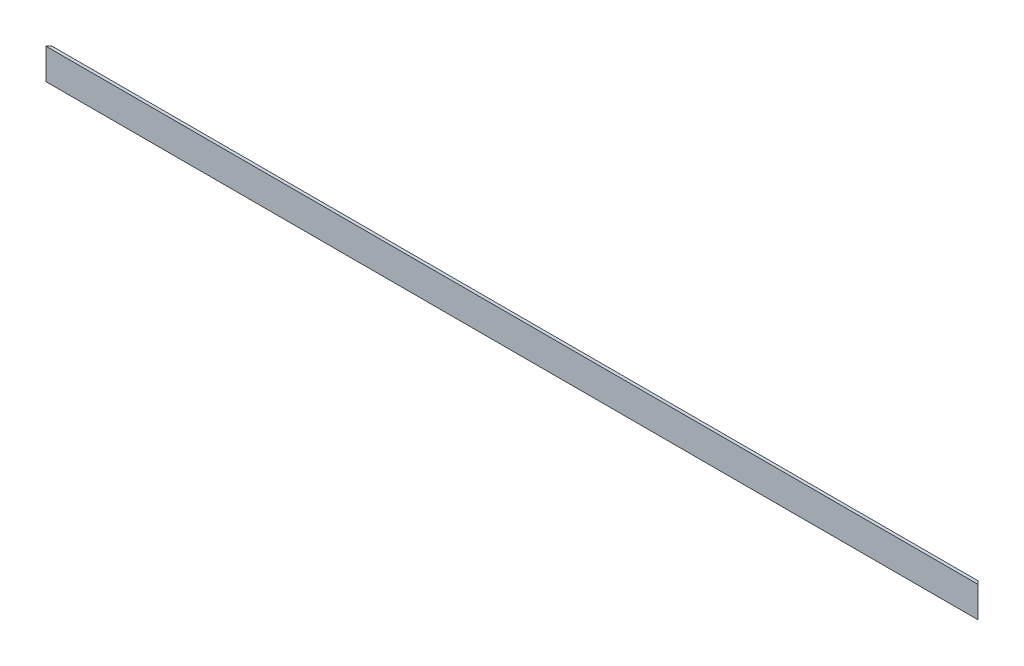
SolidWorks part; units mm, degrees
ref_plane "Спереди" through (0, 0, 0) normal (0, 0, 1) x (1, 0, 0)
ref_plane "Сверху" through (0, 0, 0) normal (0, 1, 0) x (1, 0, 0)
ref_plane "Справа" through (0, 0, 0) normal (1, 0, 0) x (0, 0, -1)
sketch "Эскиз1" plane through (0, 0, 0) normal (1, 0, 0) x (0, 0, -1)
  line L0 (0, 0) -> (0, 15)
  line L1 (0, 15) -> (1.5, 15)
  line L2 (1.5, 15) -> (1.5, 1.5)
  line L3 (1.5, 1.5) -> (15, 1.5)
  line L4 (15, 1.5) -> (15, 0)
  line L5 (15, 0) -> (0, 0)
  dimension "D1" = 15
  dimension "D2" = 15
  dimension "D3" = 1.5
  dimension "D4" = 1.5
extrude "Бобышка-Вытянуть1" add sketch "Эскиз1" along normal blind 455
sketch "Эскиз2" plane through (0, 0, 0) normal (0, -1, 0) x (1, 0, 0)
  line L0 (455, 0) -> (434.1738, -20.8262)
  line L1 (434.1738, -20.8262) -> (455, -20.8262)
  line L2 (455, -20.8262) -> (455, 0)
  dimension "D1" = 45
ref_plane "Плоскость1" through (227.5, 0, 0) normal (1, 0, 0) x (0, 0, -1)
extrude "Вырез-Вытянуть1" cut sketch "Эскиз2" against normal through all
mirror "Зеркальное отражение1" about plane through (227.5, 0, 0) normal (1, 0, 0) of "Вырез-Вытянуть1"
